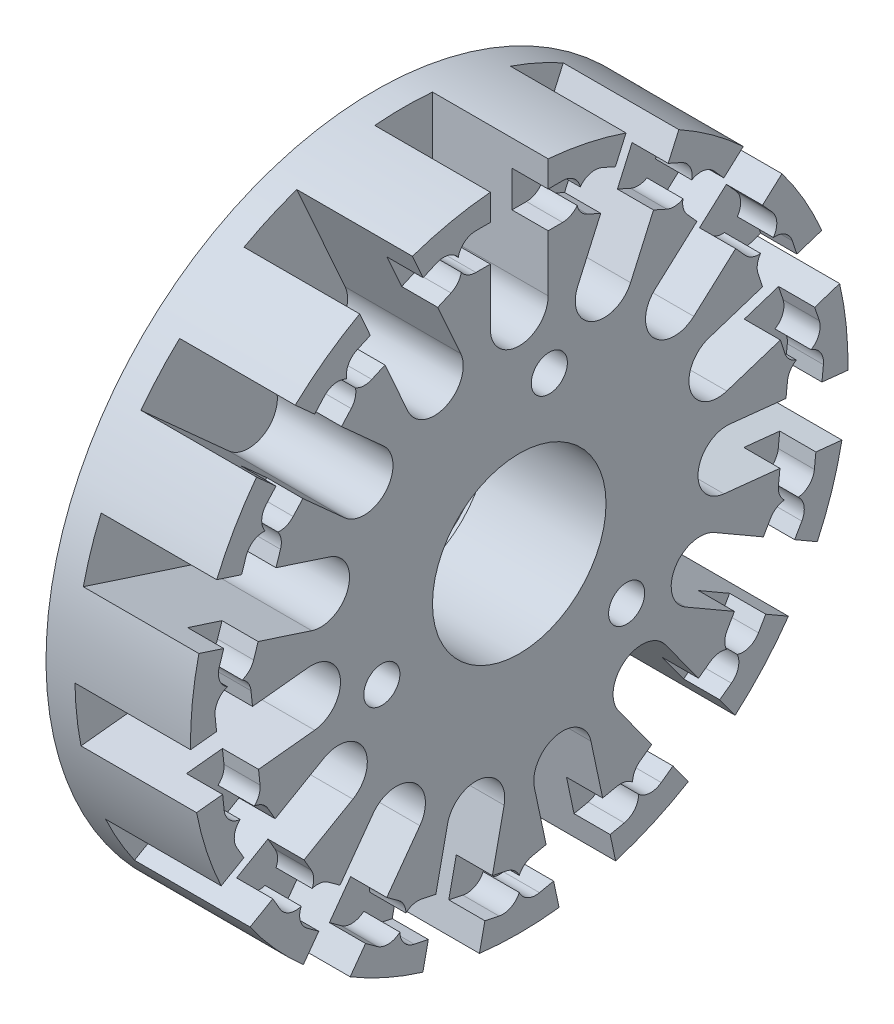
SolidWorks part; units mm, degrees
ref_plane "Front Plane" through (0, 0, 0) normal (0, 0, 1) x (1, 0, 0)
ref_plane "Top Plane" through (0, 0, 0) normal (0, 1, 0) x (1, 0, 0)
ref_plane "Right Plane" through (0, 0, 0) normal (1, 0, 0) x (0, 0, -1)
sketch "Sketch1" plane through (0, 0, 0) normal (1, 0, 0) x (0, 0, -1)
  circle A0 centre (0, 0) radius 22.75
  circle A1 centre (0, 0) radius 6.005
  dimension "D1" = 45.5
  dimension "D2" = 12.01
extrude "Boss-Extrude1" add sketch "Sketch1" along normal blind 10
sketch "Sketch2" plane through (10, 0, 0) normal (1, 0, 0) x (0, 0, -1)
  line L0 (-2, 22.75) -> (2, 22.75)
  line L1 (2, 22.75) -> (2, 14.45)
  line L2 (-2, 14.45) -> (-2, 22.75)
  arc A0 (2, 14.45) -> (-2, 14.45) centre (0, 14.45) cw
  circle A1 centre (0, 0) radius 22.75 construction
  dimension "D1" = 4
  dimension "D2" = 8.3
extrude "Cut-Extrude1" cut sketch "Sketch2" against normal blind 8
sketch "Sketch3" plane through (10, 0, 0) normal (1, 0, 0) x (0, 0, -1)
  line L0 (-3, 19.6) -> (3, 19.6) construction
  line L1 (-3, 20.85) -> (3, 20.85)
  line L2 (-3, 18.35) -> (3, 18.35)
  arc A0 (-3, 20.85) -> (-3, 18.35) centre (-3, 19.6) ccw
  arc A1 (3, 18.35) -> (3, 20.85) centre (3, 19.6) ccw
  arc A2 (-2, 14.45) -> (2, 14.45) centre (0, 14.45) ccw construction
  point P2 (0, 19.6)
  dimension "D1" = 1.25
  dimension "D2" = 5.15
  dimension "D3" = 6
extrude "Cut-Extrude2" cut sketch "Sketch3" against normal blind 2.5
pattern_circular "CirPattern1" count 15 over 360 about axis through (0, 0, 0) along (1, 0, 0) of "Cut-Extrude1", "Cut-Extrude2"
hole_wizard "Tap Drill for M3x0.5 Tap1" positions "Sketch6" profile "Sketch5" hole size "M3x0.5" standard "ANSI Metric"
sketch "Sketch6" plane through (10, 0, 0) normal (1, 0, 0) x (0, 0, -1)
  line L0 (2.0791, 9.7815) -> (0, 0) construction
  line L1 (0, 0) -> (6.005, 0) construction
  circle A2 centre (0, 0) radius 6.005 construction
  point P0 (2.0791, 9.7815)
  dimension "D1" = 78
  dimension "D2" = 10
sketch "Sketch5" plane through (10, 9.7815, -2.0791) normal (0, 1, 0) x (0, 0, -1)
  line L0 (0, 0) -> (0, 7.7511)
  line L1 (0, 7.7511) -> (1.25, 7)
  line L2 (1.25, 7) -> (1.25, 0)
  line L5 (1.25, 0) -> (0, 0)
  line L10 (0, 7.7511) -> (-1.25, 7) construction
  line L11 (0, -6.35) -> (0, 107.95) construction
  dimension "Hole Dia." = 2.5
  dimension "Hole Depth" = 7
  dimension "Drill Angle" = 118
pattern_circular "CirPattern2" count 3 over 360 about axis through (0, 0, 0) along (1, 0, 0) of "Tap Drill for M3x0.5 Tap1"
sketch "Sketch7" plane through (0, 0, 0) normal (-1, 0, 0) x (0, 0, 1)
  circle A0 centre (0, 0) radius 18.75
  dimension "D1" = 37.5
extrude "Cut-Extrude3" cut sketch "Sketch7" against normal blind 1
sketch "Sketch8" plane through (1, 0, 0) normal (-1, 0, 0) x (0, 0, 1)
  circle A0 centre (0, 0) radius 6.8
  dimension "D1" = 13.6
extrude "Cut-Extrude4" cut sketch "Sketch8" against normal blind 0.8
hole_wizard "Tap Drill for M2x0.4 Tap1" positions "Sketch10" profile "Sketch9" hole size "M2x0.4" standard "ANSI Metric"
sketch "Sketch10" plane through (0, 0, 0) normal (-1, 0, 0) x (0, 0, 1)
  line L0 (0, 0) -> (-6.005, 0) construction
  line L1 (-6.005, 0) -> (0, 0) construction
  line L3 (-4.3142, 20.2966) -> (0, 0) construction
  circle A0 centre (0, 0) radius 6.005 construction
  point P0 (-4.3142, 20.2966)
  dimension "D1" = 78
  dimension "D2" = 20.75
sketch "Sketch9" plane through (0, 20.2966, -4.3142) normal (0, 1, 0) x (0, 0, 1)
  line L0 (0, 0) -> (0, 5.9807)
  line L1 (0, 5.9807) -> (0.8, 5.5)
  line L2 (0.8, 5.5) -> (0.8, 0)
  line L5 (0.8, 0) -> (0, 0)
  line L10 (0, 5.9807) -> (-0.8, 5.5) construction
  line L11 (0, -6.35) -> (0, 107.95) construction
  dimension "Hole Dia." = 1.6
  dimension "Hole Depth" = 5.5
  dimension "Drill Angle" = 118
pattern_circular "CirPattern3" count 5 over 360 about axis through (0, 0, 0) along (1, 0, 0) of "Tap Drill for M2x0.4 Tap1"
